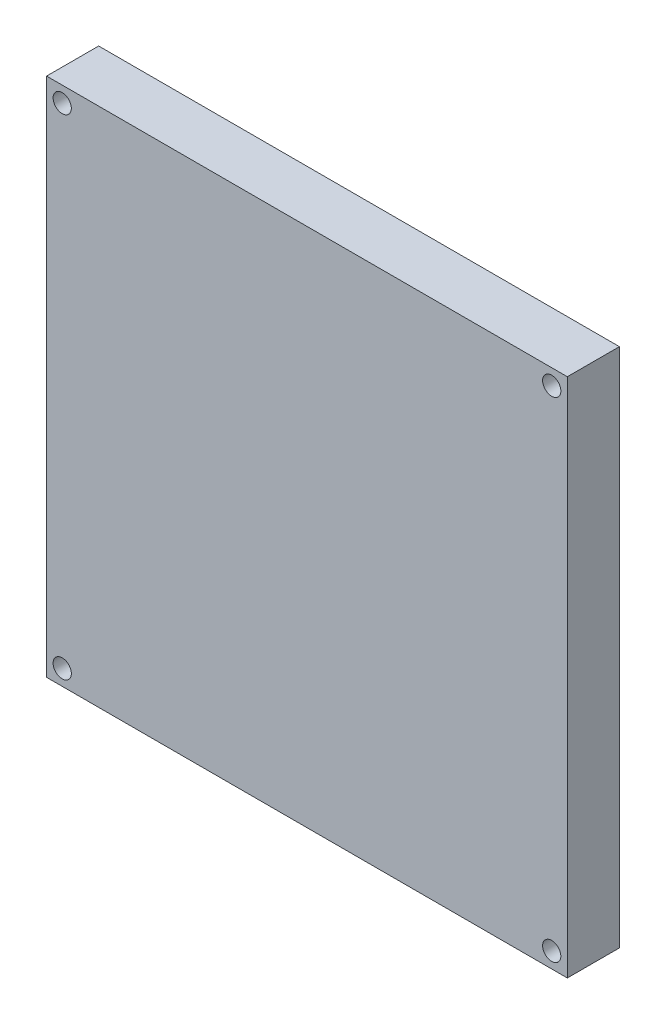
SolidWorks part; units mm, degrees
ref_plane "Front Plane" through (0, 0, 0) normal (0, 0, 1) x (1, 0, 0)
ref_plane "Top Plane" through (0, 0, 0) normal (0, 1, 0) x (1, 0, 0)
ref_plane "Right Plane" through (0, 0, 0) normal (1, 0, 0) x (0, 0, -1)
sketch "Sketch1" plane through (0, 0, 0) normal (0, 0, 1) x (1, 0, 0)
  line L1 (0, 0) -> (100, 0)
  line L2 (0, 0) -> (0, 100)
  line L3 (0, 100) -> (100, 100)
  line L4 (100, 0) -> (100, 100)
  dimension "D1" = 100
  dimension "D2" = 100
extrude "Boss-Extrude1" add sketch "Sketch1" along normal blind 10
sketch "Sketch2" plane through (0, 0, 10) normal (0, 0, 1) x (1, 0, 0)
  line L0 (50, 100) -> (50, 77.2973) construction
  line L1 (100, 100) -> (0, 100) construction
  line L2 (100, 50) -> (78.8322, 50) construction
  line L3 (100, 0) -> (100, 100) construction
  circle A0 centre (97, 97) radius 1.75
  circle A1 centre (3, 97) radius 1.75
  circle A2 centre (97, 3) radius 1.75
  circle A3 centre (3, 3) radius 1.75
  dimension "D1" = 3.5
  dimension "D2" = 3
  dimension "D3" = 94
extrude "Cut-Extrude1" cut sketch "Sketch2" against normal through all
